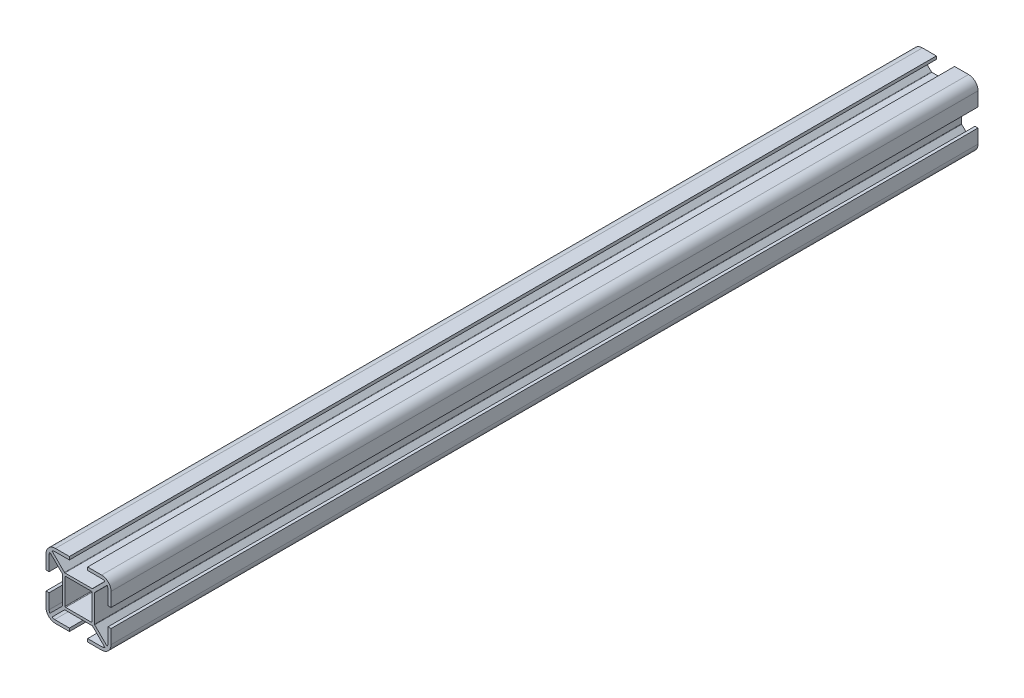
SolidWorks part; units mm, degrees
ref_plane "Спереди" through (0, 0, 0) normal (0, 0, 1) x (1, 0, 0)
ref_plane "Сверху" through (0, 0, 0) normal (0, 1, 0) x (1, 0, 0)
ref_plane "Справа" through (0, 0, 0) normal (1, 0, 0) x (0, 0, -1)
sketch "Эскиз1" plane through (0, 0, 0) normal (0, 0, 1) x (1, 0, 0)
  line L0 (-23.8723, 0) -> (-19.8723, 0) construction
  line L1 (0, -3.4409) -> (0, 20.4832) construction
  line L2 (-15, 10.65) -> (-15, 4.2)
  line L3 (-14.1209, 14.1209) -> (0, 0) construction
  line L4 (-19.4069, 4.2) -> (-7.7931, 4.2) construction
  line L5 (-10.65, 15) -> (-4.2, 15)
  line L6 (-19.8723, 0) -> (16.8962, 0) construction
  line L7 (-13.6, 4.2) -> (-13.6, 11)
  line L8 (-13.1864, 12.1965) -> (-7.4879, 6.4979)
  line L9 (-7.4, 6.2858) -> (-7.4, 0)
  line L10 (5.9, 6.2) -> (-5.9, 6.2)
  line L11 (-6.2, -0.017) -> (-6.2, 5.9)
  line L12 (-13.6, 4.2) -> (-15, 4.2)
  line L13 (-6.2858, 7.4) -> (6.2858, 7.4)
  line L14 (-12.1965, 13.1864) -> (-6.4979, 7.4879)
  line L15 (-4.2, 13.6) -> (-11, 13.6)
  line L16 (-4.2, 13.6) -> (-4.2, 15)
  line L17 (-13.6, 4.2) -> (-15, 4.2)
  line L18 (-13.6, 4.2) -> (-13.6, 11)
  line L19 (-13.1864, 12.1965) -> (-7.4879, 6.4979)
  line L20 (-7.4, 6.2858) -> (-7.4, 0)
  line L21 (-4.2, 13.6) -> (-4.2, 15)
  line L22 (0.017, 6.2) -> (-5.9, 6.2)
  line L23 (-6.2, 0) -> (-6.2, 5.9)
  line L24 (-6.2858, 7.4) -> (0, 7.4)
  line L25 (-12.1965, 13.1864) -> (-6.4979, 7.4879)
  line L26 (-4.2, 13.6) -> (-11, 13.6)
  line L27 (-15, 10.65) -> (-15, 4.2)
  line L28 (-10.65, 15) -> (-4.2, 15)
  line L29 (-15, 10.65) -> (-15, 4.2)
  line L30 (-10.65, 15) -> (-4.2, 15)
  line L31 (-13.6, 4.2) -> (-13.6, 11)
  line L32 (-13.1864, 12.1965) -> (-7.4879, 6.4979)
  line L33 (-7.4, 6.2858) -> (-7.4, 0)
  line L34 (0, 6.2) -> (-5.9, 6.2)
  line L35 (-6.2, -0.017) -> (-6.2, 5.9)
  line L36 (-13.6, 4.2) -> (-15, 4.2)
  line L37 (-6.2858, 7.4) -> (0, 7.4)
  line L38 (-12.1965, 13.1864) -> (-6.4979, 7.4879)
  line L39 (-4.2, 13.6) -> (-11, 13.6)
  line L40 (-4.2, 13.6) -> (-4.2, 15)
  line L41 (-13.6, 4.2) -> (-15, 4.2)
  line L42 (-13.6, 4.2) -> (-13.6, 11)
  line L43 (-13.1864, 12.1965) -> (-7.4879, 6.4979)
  line L44 (-7.4, 6.2858) -> (-7.4, 0)
  line L45 (-4.2, 13.6) -> (-4.2, 15)
  line L46 (0.017, 6.2) -> (-5.9, 6.2)
  line L47 (-6.2, 0) -> (-6.2, 5.9)
  line L48 (-6.2858, 7.4) -> (0, 7.4)
  line L49 (-12.1965, 13.1864) -> (-6.4979, 7.4879)
  line L50 (-4.2, 13.6) -> (-11, 13.6)
  line L51 (-15, 10.65) -> (-15, 4.2)
  line L52 (-10.65, 15) -> (-4.2, 15)
  line L53 (-15, 10.65) -> (-15, 4.2)
  line L54 (-10.65, 15) -> (-4.2, 15)
  line L55 (-13.6, 4.2) -> (-13.6, 11)
  line L56 (-13.1864, 12.1965) -> (-7.4879, 6.4979)
  line L57 (-7.4, 6.2858) -> (-7.4, 0)
  line L58 (0, 6.2) -> (-5.9, 6.2)
  line L59 (-6.2, -0.017) -> (-6.2, 5.9)
  line L60 (-13.6, 4.2) -> (-15, 4.2)
  line L61 (-6.2858, 7.4) -> (0, 7.4)
  line L62 (-12.1965, 13.1864) -> (-6.4979, 7.4879)
  line L63 (-4.2, 13.6) -> (-11, 13.6)
  line L64 (-4.2, 13.6) -> (-4.2, 15)
  line L65 (-13.6, 4.2) -> (-15, 4.2)
  line L66 (-13.6, 4.2) -> (-13.6, 11)
  line L67 (-13.1864, 12.1965) -> (-7.4879, 6.4979)
  line L68 (-7.4, 6.2858) -> (-7.4, 0)
  line L69 (-4.2, 13.6) -> (-4.2, 15)
  line L70 (0.017, 6.2) -> (-5.9, 6.2)
  line L71 (-6.2, 0) -> (-6.2, 5.9)
  line L72 (-6.2858, 7.4) -> (0, 7.4)
  line L73 (-12.1965, 13.1864) -> (-6.4979, 7.4879)
  line L74 (-4.2, 13.6) -> (-11, 13.6)
  line L75 (-15, 10.65) -> (-15, 4.2)
  line L76 (-10.65, 15) -> (-4.2, 15)
  line L77 (-15, 10.65) -> (-15, 4.2)
  line L78 (-10.65, 15) -> (-4.2, 15)
  line L79 (-13.6, 4.2) -> (-13.6, 11)
  line L80 (-13.1864, 12.1965) -> (-7.4879, 6.4979)
  line L81 (-7.4, 6.2858) -> (-7.4, 0)
  line L82 (0, 6.2) -> (-5.9, 6.2)
  line L83 (-6.2, -0.017) -> (-6.2, 5.9)
  line L84 (-13.6, 4.2) -> (-15, 4.2)
  line L85 (-6.2858, 7.4) -> (0, 7.4)
  line L86 (-12.1965, 13.1864) -> (-6.4979, 7.4879)
  line L87 (-4.2, 13.6) -> (-11, 13.6)
  line L88 (-4.2, 13.6) -> (-4.2, 15)
  line L89 (-13.6, 4.2) -> (-15, 4.2)
  line L90 (-13.6, 4.2) -> (-13.6, 11)
  line L91 (-13.1864, 12.1965) -> (-7.4879, 6.4979)
  line L92 (-7.4, 6.2858) -> (-7.4, 0)
  line L93 (-4.2, 13.6) -> (-4.2, 15)
  line L94 (0.017, 6.2) -> (-5.9, 6.2)
  line L95 (-6.2, 0) -> (-6.2, 5.9)
  line L96 (-6.2858, 7.4) -> (0, 7.4)
  line L97 (-12.1965, 13.1864) -> (-6.4979, 7.4879)
  line L98 (-4.2, 13.6) -> (-11, 13.6)
  line L99 (-15, 10.65) -> (-15, 4.2)
  line L100 (-10.65, 15) -> (-4.2, 15)
  line L101 (13.6, 4.2) -> (15, 4.2)
  line L102 (4.2, 13.6) -> (4.2, 15)
  line L103 (10.65, 15) -> (4.2, 15)
  line L104 (4.2, 13.6) -> (11, 13.6)
  line L105 (12.1965, 13.1864) -> (6.4979, 7.4879)
  line L106 (6.2, -0.017) -> (6.2, 5.9)
  line L107 (7.4, 6.2858) -> (7.4, 0)
  line L108 (13.1864, 12.1965) -> (7.4879, 6.4979)
  line L109 (13.6, 4.2) -> (13.6, 11)
  line L110 (15, 10.65) -> (15, 4.2)
  line L111 (-10.65, -15) -> (-4.2, -15)
  line L112 (13.6, -4.2) -> (13.6, -11)
  line L113 (-12.1965, -13.1864) -> (-6.4979, -7.4879)
  line L114 (-6.2858, -7.4) -> (6.2858, -7.4)
  line L115 (0.017, -6.2) -> (-5.9, -6.2)
  line L116 (-13.1864, -12.1965) -> (-7.4879, -6.4979)
  line L117 (4.2, -13.6) -> (11, -13.6)
  line L118 (-15, -10.65) -> (-15, -4.2)
  line L119 (-13.6, -4.2) -> (-15, -4.2)
  line L120 (-4.2, -13.6) -> (-4.2, -15)
  line L121 (-15, 10.65) -> (-15, 4.2)
  line L122 (-10.65, 15) -> (-4.2, 15)
  line L123 (-13.6, 4.2) -> (-13.6, 11)
  line L124 (-13.1864, 12.1965) -> (-7.4879, 6.4979)
  line L125 (-7.4, 6.2858) -> (-7.4, 0)
  line L126 (0, 6.2) -> (-5.9, 6.2)
  line L127 (-6.2, -0.017) -> (-6.2, 5.9)
  line L128 (-13.6, 4.2) -> (-15, 4.2)
  line L129 (-6.2858, 7.4) -> (0, 7.4)
  line L130 (-12.1965, 13.1864) -> (-6.4979, 7.4879)
  line L131 (-4.2, 13.6) -> (-11, 13.6)
  line L132 (-4.2, 13.6) -> (-4.2, 15)
  line L133 (-13.6, 4.2) -> (-15, 4.2)
  line L134 (-13.6, 4.2) -> (-13.6, 11)
  line L135 (-13.1864, 12.1965) -> (-7.4879, 6.4979)
  line L136 (-7.4, 6.2858) -> (-7.4, 0)
  line L137 (-4.2, 13.6) -> (-4.2, 15)
  line L138 (0.017, 6.2) -> (-5.9, 6.2)
  line L139 (-6.2, 0) -> (-6.2, 5.9)
  line L140 (-6.2858, 7.4) -> (0, 7.4)
  line L141 (-12.1965, 13.1864) -> (-6.4979, 7.4879)
  line L142 (-4.2, 13.6) -> (-11, 13.6)
  line L143 (-15, 10.65) -> (-15, 4.2)
  line L144 (-10.65, 15) -> (-4.2, 15)
  line L145 (-15, 10.65) -> (-15, 4.2)
  line L146 (-10.65, 15) -> (-4.2, 15)
  line L147 (-13.6, 4.2) -> (-13.6, 11)
  line L148 (-13.1864, 12.1965) -> (-7.4879, 6.4979)
  line L149 (-7.4, 6.2858) -> (-7.4, 0)
  line L150 (0, 6.2) -> (-5.9, 6.2)
  line L151 (-6.2, -0.017) -> (-6.2, 5.9)
  line L152 (-13.6, 4.2) -> (-15, 4.2)
  line L153 (-6.2858, 7.4) -> (0, 7.4)
  line L154 (-12.1965, 13.1864) -> (-6.4979, 7.4879)
  line L155 (-4.2, 13.6) -> (-11, 13.6)
  line L156 (-4.2, 13.6) -> (-4.2, 15)
  line L157 (-13.6, 4.2) -> (-15, 4.2)
  line L158 (-13.6, 4.2) -> (-13.6, 11)
  line L159 (-13.1864, 12.1965) -> (-7.4879, 6.4979)
  line L160 (-7.4, 6.2858) -> (-7.4, 0)
  line L161 (-4.2, 13.6) -> (-4.2, 15)
  line L162 (0.017, 6.2) -> (-5.9, 6.2)
  line L163 (-6.2, 0) -> (-6.2, 5.9)
  line L164 (-6.2858, 7.4) -> (0, 7.4)
  line L165 (-12.1965, 13.1864) -> (-6.4979, 7.4879)
  line L166 (-4.2, 13.6) -> (-11, 13.6)
  line L167 (-15, 10.65) -> (-15, 4.2)
  line L168 (-10.65, 15) -> (-4.2, 15)
  line L169 (-15, 10.65) -> (-15, 4.2)
  line L170 (-10.65, 15) -> (-4.2, 15)
  line L171 (-13.6, 4.2) -> (-13.6, 11)
  line L172 (-13.1864, 12.1965) -> (-7.4879, 6.4979)
  line L173 (-7.4, 6.2858) -> (-7.4, 0)
  line L174 (0, 6.2) -> (-5.9, 6.2)
  line L175 (-6.2, -0.017) -> (-6.2, 5.9)
  line L176 (-13.6, 4.2) -> (-15, 4.2)
  line L177 (-6.2858, 7.4) -> (0, 7.4)
  line L178 (-12.1965, 13.1864) -> (-6.4979, 7.4879)
  line L179 (-4.2, 13.6) -> (-11, 13.6)
  line L180 (-4.2, 13.6) -> (-4.2, 15)
  line L181 (-13.6, 4.2) -> (-15, 4.2)
  line L182 (-13.6, 4.2) -> (-13.6, 11)
  line L183 (-13.1864, 12.1965) -> (-7.4879, 6.4979)
  line L184 (-7.4, 6.2858) -> (-7.4, 0)
  line L185 (-4.2, 13.6) -> (-4.2, 15)
  line L186 (0.017, 6.2) -> (-5.9, 6.2)
  line L187 (-6.2, 0) -> (-6.2, 5.9)
  line L188 (-6.2858, 7.4) -> (0, 7.4)
  line L189 (-12.1965, 13.1864) -> (-6.4979, 7.4879)
  line L190 (-4.2, 13.6) -> (-11, 13.6)
  line L191 (-15, 10.65) -> (-15, 4.2)
  line L192 (-10.65, 15) -> (-4.2, 15)
  line L193 (-15, 10.65) -> (-15, 4.2)
  line L194 (-10.65, 15) -> (-4.2, 15)
  line L195 (-13.6, 4.2) -> (-13.6, 11)
  line L196 (-13.1864, 12.1965) -> (-7.4879, 6.4979)
  line L197 (-7.4, 6.2858) -> (-7.4, 0)
  line L198 (0, 6.2) -> (-5.9, 6.2)
  line L199 (-6.2, -0.017) -> (-6.2, 5.9)
  line L200 (-13.6, 4.2) -> (-15, 4.2)
  line L201 (-6.2858, 7.4) -> (0, 7.4)
  line L202 (-12.1965, 13.1864) -> (-6.4979, 7.4879)
  line L203 (-4.2, 13.6) -> (-11, 13.6)
  line L204 (-4.2, 13.6) -> (-4.2, 15)
  line L205 (-13.6, 4.2) -> (-15, 4.2)
  line L206 (-13.6, 4.2) -> (-13.6, 11)
  line L207 (-13.1864, 12.1965) -> (-7.4879, 6.4979)
  line L208 (-7.4, 6.2858) -> (-7.4, -6.2858)
  line L209 (-4.2, 13.6) -> (-4.2, 15)
  line L210 (0.017, 6.2) -> (-5.9, 6.2)
  line L211 (-6.2, -5.9) -> (-6.2, 5.9)
  line L212 (-6.2858, 7.4) -> (0, 7.4)
  line L213 (-12.1965, 13.1864) -> (-6.4979, 7.4879)
  line L214 (-4.2, 13.6) -> (-11, 13.6)
  line L215 (-15, 10.65) -> (-15, 4.2)
  line L216 (-10.65, 15) -> (-4.2, 15)
  line L217 (7.4, 6.2858) -> (7.4, -6.2858)
  line L218 (6.2, -5.9) -> (6.2, 5.9)
  line L219 (4.2, -13.6) -> (4.2, -15)
  line L220 (13.6, -4.2) -> (15, -4.2)
  line L221 (15, -10.65) -> (15, -4.2)
  line L222 (-4.2, -13.6) -> (-11, -13.6)
  line L223 (13.1864, -12.1965) -> (7.4879, -6.4979)
  line L224 (-0.017, -6.2) -> (5.9, -6.2)
  line L225 (12.1965, -13.1864) -> (6.4979, -7.4879)
  line L226 (-13.6, -4.2) -> (-13.6, -11)
  line L227 (10.65, -15) -> (4.2, -15)
  arc A0 (-15, 10.65) -> (-10.65, 15) centre (-10.65, 10.65) cw
  arc A1 (-7.4879, 6.4979) -> (-7.4, 6.2858) centre (-7.7, 6.2858) cw
  arc A2 (-6.2858, 7.4) -> (-6.4979, 7.4879) centre (-6.2858, 7.7) cw
  arc A3 (-5.9, 6.2) -> (-6.2, 5.9) centre (-5.9, 5.9) ccw
  arc A4 (-13.1864, 12.1965) -> (-13.6, 11) centre (-10.65, 10.65) ccw
  arc A5 (11, 13.6) -> (12.1965, 13.1864) centre (10.65, 10.65) cw
  arc A6 (13.1864, 12.1965) -> (13.6, 11) centre (10.65, 10.65) cw
  arc A7 (13.1864, -12.1965) -> (13.6, -11) centre (10.65, -10.65) ccw
  arc A8 (-7.4, 6.2858) -> (-7.4879, 6.4979) centre (-7.7, 6.2858) ccw
  arc A9 (-6.4979, 7.4879) -> (-6.2858, 7.4) centre (-6.2858, 7.7) ccw
  arc A10 (-7.4879, 6.4979) -> (-7.4, 6.2858) centre (-7.7, 6.2858) cw
  arc A11 (-6.2858, 7.4) -> (-6.4979, 7.4879) centre (-6.2858, 7.7) cw
  arc A12 (11, -13.6) -> (12.1965, -13.1864) centre (10.65, -10.65) ccw
  arc A13 (-11, -13.6) -> (-12.1965, -13.1864) centre (-10.65, -10.65) cw
  arc A14 (-13.1864, -12.1965) -> (-13.6, -11) centre (-10.65, -10.65) cw
  arc A16 (-7.4, 6.2858) -> (-7.4879, 6.4979) centre (-7.7, 6.2858) ccw
  arc A17 (-6.4979, 7.4879) -> (-6.2858, 7.4) centre (-6.2858, 7.7) ccw
  arc A18 (-7.4879, 6.4979) -> (-7.4, 6.2858) centre (-7.7, 6.2858) cw
  arc A19 (-6.2858, 7.4) -> (-6.4979, 7.4879) centre (-6.2858, 7.7) cw
  arc A24 (-7.4, 6.2858) -> (-7.4879, 6.4979) centre (-7.7, 6.2858) ccw
  arc A25 (-6.4979, 7.4879) -> (-6.2858, 7.4) centre (-6.2858, 7.7) ccw
  arc A26 (-7.4879, 6.4979) -> (-7.4, 6.2858) centre (-7.7, 6.2858) cw
  arc A27 (-6.2858, 7.4) -> (-6.4979, 7.4879) centre (-6.2858, 7.7) cw
  arc A32 (-7.4, 6.2858) -> (-7.4879, 6.4979) centre (-7.7, 6.2858) ccw
  arc A33 (-6.4979, 7.4879) -> (-6.2858, 7.4) centre (-6.2858, 7.7) ccw
  arc A35 (6.2858, 7.4) -> (6.4979, 7.4879) centre (6.2858, 7.7) ccw
  arc A36 (5.9, 6.2) -> (6.2, 5.9) centre (5.9, 5.9) cw
  arc A38 (15, 10.65) -> (10.65, 15) centre (10.65, 10.65) ccw
  arc A39 (7.4879, 6.4979) -> (7.4, 6.2858) centre (7.7, 6.2858) ccw
  arc A40 (-6.4979, -7.4879) -> (-6.2858, -7.4) centre (-6.2858, -7.7) cw
  arc A41 (-10.65, -15) -> (-15, -10.65) centre (-10.65, -10.65) cw
  arc A43 (-6.2, -5.9) -> (-5.9, -6.2) centre (-5.9, -5.9) ccw
  arc A44 (-7.4, -6.2858) -> (-7.4879, -6.4979) centre (-7.7, -6.2858) cw
  arc A46 (-7.4879, 6.4979) -> (-7.4, 6.2858) centre (-7.7, 6.2858) cw
  arc A47 (-6.2858, 7.4) -> (-6.4979, 7.4879) centre (-6.2858, 7.7) cw
  arc A52 (-7.4, 6.2858) -> (-7.4879, 6.4979) centre (-7.7, 6.2858) ccw
  arc A53 (-6.4979, 7.4879) -> (-6.2858, 7.4) centre (-6.2858, 7.7) ccw
  arc A54 (-7.4879, 6.4979) -> (-7.4, 6.2858) centre (-7.7, 6.2858) cw
  arc A55 (-6.2858, 7.4) -> (-6.4979, 7.4879) centre (-6.2858, 7.7) cw
  arc A60 (-7.4, 6.2858) -> (-7.4879, 6.4979) centre (-7.7, 6.2858) ccw
  arc A61 (-6.4979, 7.4879) -> (-6.2858, 7.4) centre (-6.2858, 7.7) ccw
  arc A62 (-7.4879, 6.4979) -> (-7.4, 6.2858) centre (-7.7, 6.2858) cw
  arc A63 (-6.2858, 7.4) -> (-6.4979, 7.4879) centre (-6.2858, 7.7) cw
  arc A68 (-7.4, 6.2858) -> (-7.4879, 6.4979) centre (-7.7, 6.2858) ccw
  arc A69 (-6.4979, 7.4879) -> (-6.2858, 7.4) centre (-6.2858, 7.7) ccw
  arc A70 (-7.4879, 6.4979) -> (-7.4, 6.2858) centre (-7.7, 6.2858) cw
  arc A71 (-6.2858, 7.4) -> (-6.4979, 7.4879) centre (-6.2858, 7.7) cw
  arc A76 (-7.4, 6.2858) -> (-7.4879, 6.4979) centre (-7.7, 6.2858) ccw
  arc A77 (-6.4979, 7.4879) -> (-6.2858, 7.4) centre (-6.2858, 7.7) ccw
  arc A79 (7.4, -6.2858) -> (7.4879, -6.4979) centre (7.7, -6.2858) ccw
  arc A80 (6.2, -5.9) -> (5.9, -6.2) centre (5.9, -5.9) cw
  arc A82 (10.65, -15) -> (15, -10.65) centre (10.65, -10.65) ccw
  arc A83 (6.4979, -7.4879) -> (6.2858, -7.4) centre (6.2858, -7.7) ccw
  arc A85 (-11, 13.6) -> (-12.1965, 13.1864) centre (-10.65, 10.65) ccw
  point P0 (0, 0)
  point P29 (-7.4, 6.4101)
  point P32 (-6.4101, 7.4)
  point P35 (-6.2, 6.2)
  point P38 (-12.6101, 13.6)
  point P41 (-13.6, 12.6101)
  point P115 (0, -7.4)
  dimension "D1" = 0.3
  dimension "D8" = 4.35
  dimension "D2" = 15
  dimension "D3" = 4.2
  dimension "D4" = 7.6
  dimension "D5" = 12.4
  dimension "D6" = 1.4
  dimension "D7" = 1.4
extrude "Бобышка-Вытянуть1" add sketch "Эскиз1" along normal blind 400
